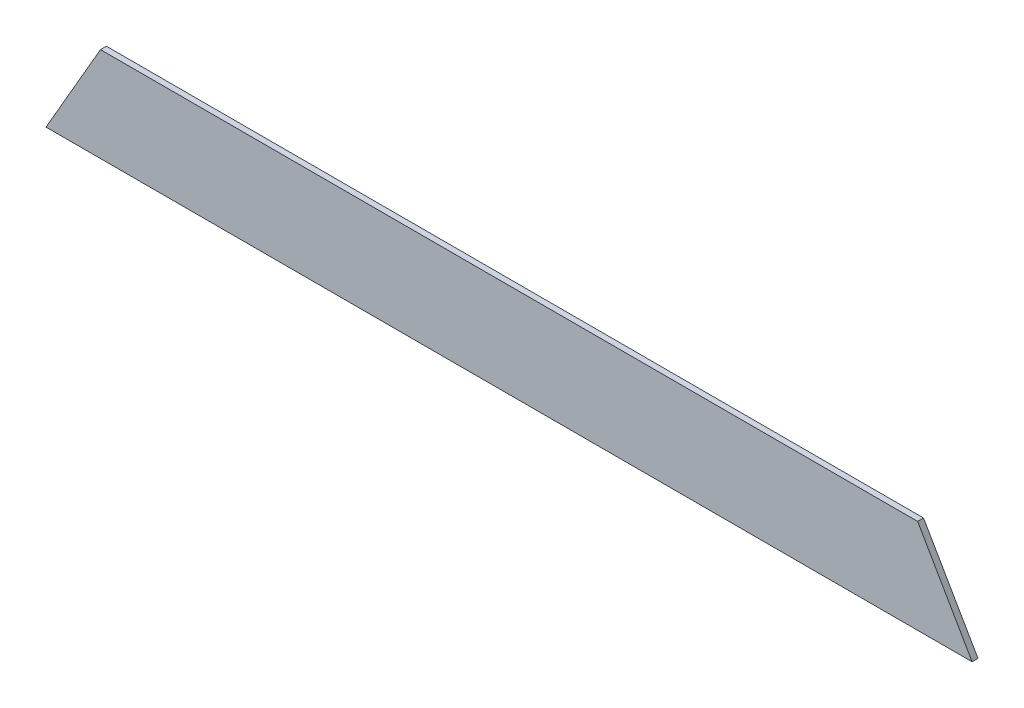
SolidWorks part; units mm, degrees
ref_plane "Front Plane" through (0, 0, 0) normal (0, 0, 1) x (1, 0, 0)
ref_plane "Top Plane" through (0, 0, 0) normal (0, 1, 0) x (1, 0, 0)
ref_plane "Right Plane" through (0, 0, 0) normal (1, 0, 0) x (0, 0, -1)
sketch "Sketch1" plane through (0, 0, 0) normal (0, 0, 1) x (1, 0, 0)
  line L1 (0, 0) -> (439.9534, 0)
  line L2 (0, 0) -> (0, 50.8)
  line L3 (0, 50.8) -> (439.9534, 50.8)
  line L4 (439.9534, 0) -> (439.9534, 50.8)
  dimension "D1" = 439.9534
  dimension "D2" = 50.8
extrude "Boss-Extrude1" add sketch "Sketch1" along normal blind 3.175
sketch "Sketch2" plane through (0, 0, 3.175) normal (0, 0, 1) x (1, 0, 0)
  line L0 (0, 50.8) -> (-29.3294, 0)
  line L1 (-29.3294, 0) -> (0, 0)
  line L2 (0, 0) -> (0, 50.8)
  line L3 (219.9767, 50.8) -> (219.9767, 0) construction
  line L4 (439.9534, 50.8) -> (0, 50.8) construction
  line L5 (0, 0) -> (439.9534, 0) construction
  line L6 (469.2828, 0) -> (439.9534, 0)
  line L7 (439.9534, 50.8) -> (469.2828, 0)
  line L8 (439.9534, 0) -> (439.9534, 50.8)
  dimension "D1" = 30
extrude "Boss-Extrude2" add sketch "Sketch2" against normal up to surface (3.175 mm away) up to face at (219.9767, 25.4, 0)
